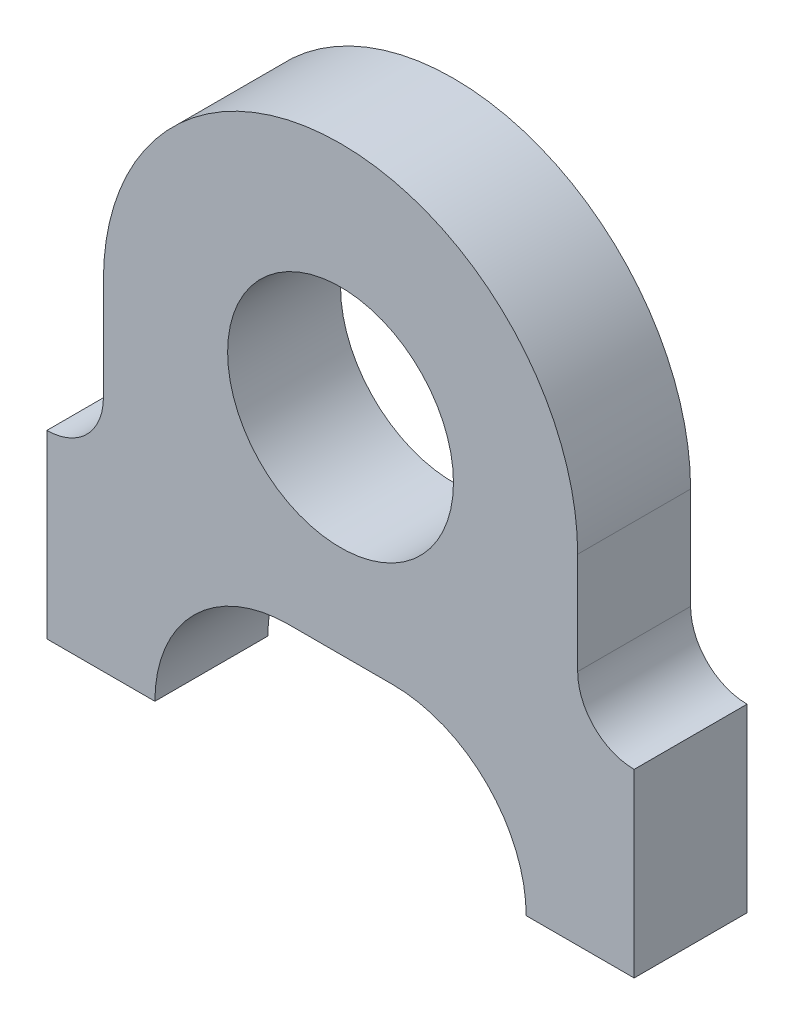
SolidWorks part; units mm, degrees
material "1023 Carbon Steel Sheet (SS)"
ref_plane "Front Plane" through (0, 0, 0) normal (0, 0, 1) x (1, 0, 0)
ref_plane "Top Plane" through (0, 0, 0) normal (0, 1, 0) x (1, 0, 0)
ref_plane "Right Plane" through (0, 0, 0) normal (1, 0, 0) x (0, 0, -1)
sketch "Sketch1" plane through (0, 0, 0) normal (0, 0, 1) x (1, 0, 0)
  line L0 (-13.335, 0) -> (-13.335, -5.715)
  line L1 (13.335, 0) -> (13.335, -5.715)
  line L2 (0, 0) -> (0, -102.3391) construction
  line L3 (10.4394, -19.05) -> (16.51, -19.05)
  line L4 (-16.51, -8.89) -> (-16.51, -19.05)
  line L5 (-16.51, -19.05) -> (-10.4394, -19.05)
  line L6 (16.51, -8.89) -> (16.51, -19.05)
  line L9 (-2.9376, -11.5482) -> (2.9376, -11.5482)
  circle A0 centre (0, 0) radius 6.35
  arc A1 (13.335, 0) -> (-13.335, 0) centre (0, 0) ccw
  arc A2 (-16.51, -8.89) -> (-13.335, -5.715) centre (-16.51, -5.715) ccw
  arc A3 (16.51, -8.89) -> (13.335, -5.715) centre (16.51, -5.715) cw
  arc A4 (-10.4394, -19.05) -> (-2.9376, -11.5482) centre (-2.9376, -19.05) cw
  arc A5 (10.4394, -19.05) -> (2.9376, -11.5482) centre (2.9376, -19.05) ccw
  point P7 (0, -19.05)
  point P11 (0, -8.89)
  point P20 (0, -11.5482)
  dimension "D1" = 12.7
  dimension "D2" = 26.67
  dimension "D5" = 32.385
  dimension "D3" = 10.16
  dimension "D4" = 33.02
  dimension "D6" = 6.0706
extrude "Boss-Extrude1" add sketch "Sketch1" along normal blind 6.35
hole_wizard "Tap Drill for #6-32 Tap1" positions "Sketch3" profile "Sketch2" hole size "#6-32" standard "ANSI Inch"
sketch "Sketch3" plane through (0, -19.05, 0) normal (0, -1, 0) x (-1, 0, 0)
  point P0 (13.4747, -3.175)
sketch "Sketch2" plane through (-13.4747, -19.05, 3.175) normal (1, 0, 0) x (0, 0, -1)
  line L0 (0, 0) -> (0, 8.4327)
  line L1 (0, 8.4327) -> (1.3525, 7.62)
  line L2 (1.3525, 7.62) -> (1.3525, 0)
  line L5 (1.3525, 0) -> (0, 0)
  line L10 (0, 8.4327) -> (-1.3526, 7.62) construction
  line L11 (0, -6.35) -> (0, 107.95) construction
  dimension "Hole Dia." = 2.7051
  dimension "Hole Depth" = 7.62
  dimension "Drill Angle" = 118
mirror "Mirror1" about plane through (0, 0, 0) normal (1, 0, 0) of "Tap Drill for #6-32 Tap1"
